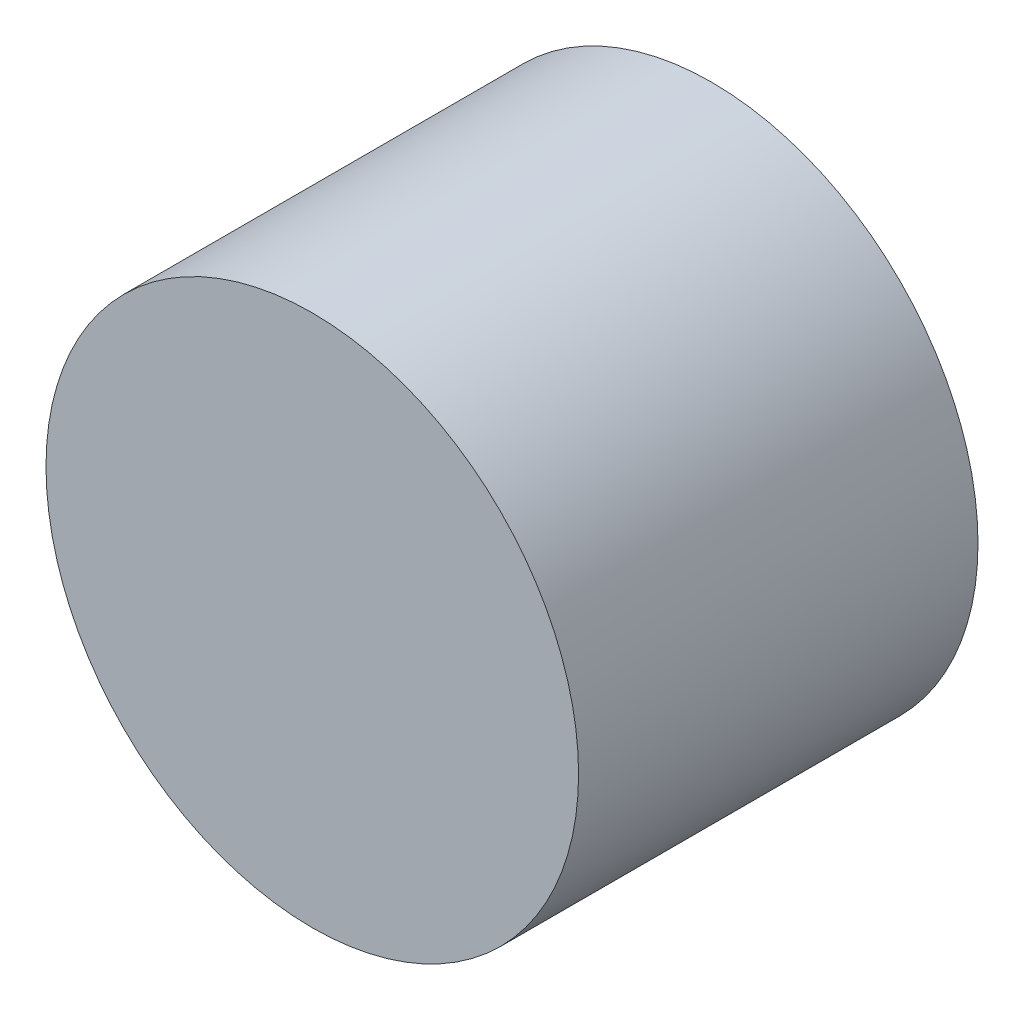
SolidWorks part; units mm, degrees
ref_plane "前视基准面" through (0, 0, 0) normal (0, 0, 1) x (1, 0, 0)
ref_plane "上视基准面" through (0, 0, 0) normal (0, 1, 0) x (1, 0, 0)
ref_plane "右视基准面" through (0, 0, 0) normal (1, 0, 0) x (0, 0, -1)
sketch "草图1" plane through (0, 0, 0) normal (0, 0, 1) x (1, 0, 0)
  circle A0 centre (0, 0) radius 4
  dimension "D1" = 8
extrude "凸台-拉伸1" add sketch "草图1" along normal blind 6
sketch "草图3" plane through (0, 0, 0) normal (0, 0, -1) x (-1, 0, 0)
  line L1 (2.9986, -0.0917) -> (1.5787, 2.551)
  line L2 (1.5787, 2.551) -> (-1.4199, 2.6427)
  line L3 (-1.4199, 2.6427) -> (-2.9986, 0.0917)
  line L4 (-2.9986, 0.0917) -> (-1.5787, -2.551)
  line L5 (-1.5787, -2.551) -> (1.4199, -2.6427)
  line L6 (1.4199, -2.6427) -> (2.9986, -0.0917)
  circle A0 centre (0, 0) radius 3 construction
  circle A1 centre (0, 0) radius 2.5981 construction
  dimension "D1" = 6
extrude "切除-拉伸1" cut sketch "草图3" against normal blind 3
